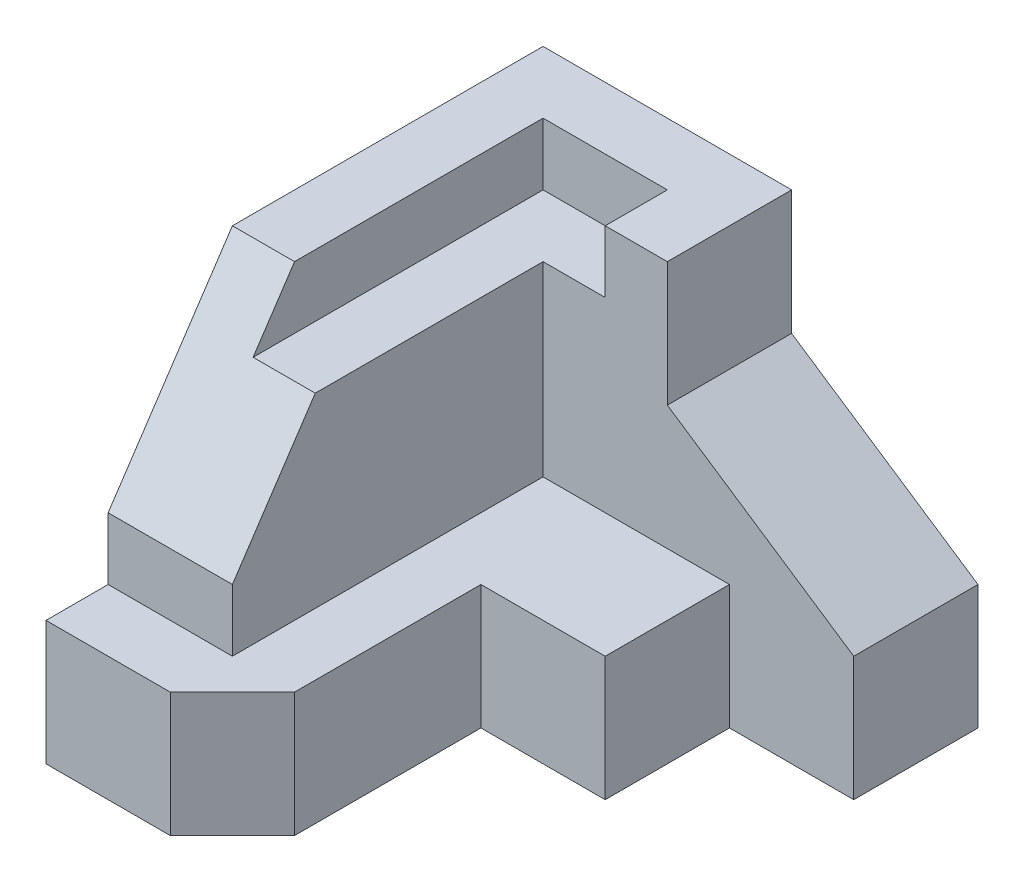
SolidWorks part; units mm, degrees
ref_plane "Front Plane" through (0, 0, 0) normal (0, 0, 1) x (1, 0, 0)
ref_plane "Top Plane" through (0, 0, 0) normal (0, 1, 0) x (1, 0, 0)
ref_plane "Right Plane" through (0, 0, 0) normal (1, 0, 0) x (0, 0, -1)
sketch "Sketch1" plane through (0, 0, 0) normal (0, 0, 1) x (1, 0, 0)
  line L1 (3.5, -3) -> (-3.5, -3)
  line L2 (3.5, -3) -> (3.5, 3)
  line L3 (3.5, 3) -> (-3.5, 3)
  line L4 (-3.5, -3) -> (-3.5, 3)
  line L5 (3.5, -3) -> (-3.5, 3) construction
  line L6 (3.5, 3) -> (-3.5, -3) construction
  point P0 (0, 0)
  dimension "D1" = 7
  dimension "D2" = 6
extrude "Boss-Extrude2" add sketch "Sketch1" along normal blind 8
sketch "Sketch4" plane through (0, 3, 0) normal (0, 1, 0) x (1, 0, 0)
  line L0 (3.5, -2) -> (1.5, -2)
  line L1 (3.5, -8) -> (3.5, 0) construction
  line L2 (1.5, -2) -> (1.5, -4)
  line L3 (1.5, -4) -> (-0.5, -4)
  line L4 (-0.5, -4) -> (-0.5, -7)
  line L5 (-0.5, -7) -> (-1.5, -8)
  line L6 (3.5, -8) -> (-3.5, -8) construction
  line L7 (-1.5, -8) -> (3.5, -8)
  line L8 (3.5, -8) -> (3.5, -2)
  dimension "D1" = 2
  dimension "D2" = 2
  dimension "D3" = 2
  dimension "D4" = 2
  dimension "D5" = 3
  dimension "D6" = 5
extrude "Cut-Extrude2" cut sketch "Sketch4" against normal through all
sketch "Sketch5" plane through (0, 3, 0) normal (0, 1, 0) x (1, 0, 0)
  line L0 (1.5, -4) -> (1.5, -2)
  line L1 (1.5, -2) -> (-1.5, -2)
  line L2 (-1.5, -2) -> (-1.5, -7)
  line L3 (-1.5, -7) -> (-3.5, -7)
  line L4 (-3.5, -8) -> (-3.5, 0) construction
  line L5 (-3.5, -7) -> (-3.5, -8)
  line L6 (-3.5, -8) -> (-1.5, -8)
  line L7 (-1.5, -8) -> (-0.5, -7)
  line L8 (-0.5, -7) -> (-0.5, -4)
  line L9 (-0.5, -4) -> (1.5, -4)
  dimension "D1" = 3
  dimension "D2" = 1
extrude "Cut-Extrude3" cut sketch "Sketch5" against normal blind 4
sketch "Sketch6" plane through (0, 0, 0) normal (0, 0, -1) x (-1, 0, 0)
  line L0 (-3.5, -1) -> (-0.5, 1)
  line L1 (-3.5, -3) -> (-3.5, 3) construction
  line L2 (-0.5, 1) -> (-0.5, 3)
  line L3 (-3.5, 3) -> (3.5, 3) construction
  line L4 (-0.5, 3) -> (-3.5, 3)
  line L5 (-3.5, 3) -> (-3.5, -1)
  dimension "D1" = 2
  dimension "D2" = 2
  dimension "D3" = 3
extrude "Cut-Extrude4" cut sketch "Sketch6" against normal blind 2
sketch "Sketch7" plane through (0, 3, 0) normal (0, 1, 0) x (1, 0, 0)
  line L0 (-0.5, -2) -> (-0.5, -1)
  line L1 (0.5, -2) -> (-1.5, -2) construction
  line L2 (-0.5, -1) -> (-2.5, -1)
  line L3 (-2.5, -1) -> (-2.5, -6)
  line L4 (-2.5, -6) -> (-1.5, -6)
  line L5 (-1.5, -2) -> (-1.5, -7) construction
  line L6 (-1.5, -6) -> (-1.5, -2)
  line L7 (-1.5, -2) -> (-0.5, -2)
  line L8 (-3.5, -7) -> (-3.5, 0) construction
  dimension "D1" = 1
  dimension "D2" = 1
  dimension "D3" = 4
extrude "Cut-Extrude5" cut sketch "Sketch7" against normal blind 1
sketch "Sketch8" plane through (0, 0, 7) normal (0, 0, 1) x (1, 0, 0)
  line L0 (-1.5, 0) -> (-3.5, 0)
  line L1 (-1.5, -1) -> (-1.5, 3) construction
  line L2 (-3.5, -1) -> (-3.5, 3) construction
  line L3 (-3.5, -1) -> (-1.5, -1) construction
  dimension "D1" = 1
sketch "Sketch9" plane through (0, 3, 0) normal (0, 1, 0) x (1, 0, 0)
  line L0 (-3.5, -5) -> (-1.5, -5)
  line L1 (-3.5, -7) -> (-3.5, 0) construction
  line L2 (0.5, 0) -> (-3.5, 0) construction
  line L3 (-1.5, -6) -> (-1.5, -2) construction
  dimension "D1" = 5
ref_plane "Plane1" through (0, 3.2308, 4.8462) normal (0, -0.5547, -0.8321) x (-1, 0, 0)
sketch "Sketch10" plane through (0, 3.2308, 4.8462) normal (0, -0.5547, -0.8321) x (-1, 0, 0)
  line L0 (3.5, -0.2774) -> (1.5, -0.2774)
  line L1 (1.5, -0.2774) -> (1.5, -3.8829)
  line L2 (1.5, -3.8829) -> (3.5, -3.8829)
  line L3 (3.5, -3.8829) -> (3.5, -0.2774)
extrude "Cut-Extrude6" cut sketch "Sketch10" against normal through all
